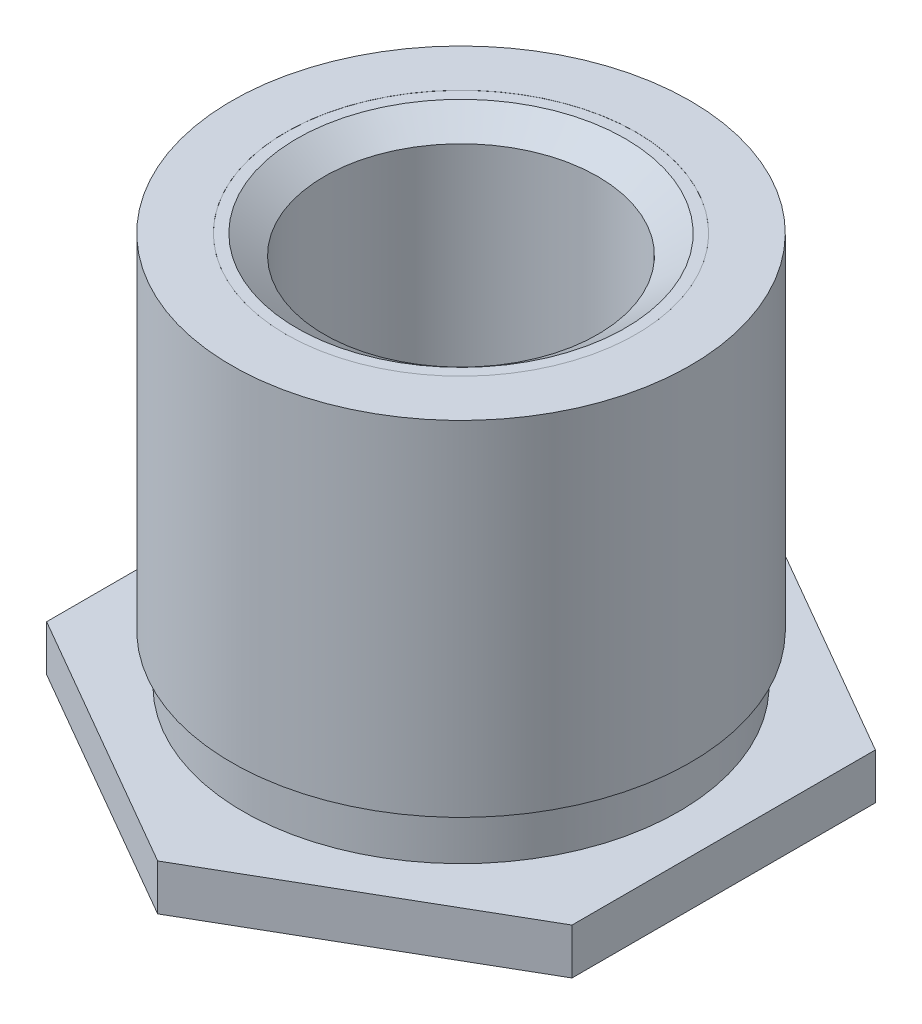
SolidWorks part; units mm, degrees
ref_plane "Plane1" through (0, 0, 0) normal (0, 0, 1) x (1, 0, 0)
ref_plane "Plane2" through (0, 0, 0) normal (0, 1, 0) x (1, 0, 0)
ref_plane "Plane3" through (0, 0, 0) normal (1, 0, 0) x (0, 0, -1)
sketch "BodySke" plane through (0, 0, 0) normal (0, 0, 1) x (1, 0, 0)
  line L0 (2.095, 0) -> (2.784, 0)
  line L1 (2.784, 0) -> (2.784, 0.419)
  line L2 (2.784, 0.419) -> (1.9903, 0.419)
  line L3 (1.25, 4) -> (1.25, 0.006)
  line L4 (2.095, 0.8589) -> (1.9903, 0.8589)
  line L5 (1.9903, 0.8589) -> (1.9903, 0.419)
  line L6 (2.095, 0.0025) -> (2.095, 0)
  line L7 (1.016, 3.5) -> (3.6522, 3.5) construction
  line L8 (2.095, 4) -> (1.25, 4)
  line L9 (0, 0) -> (0, 15.24) construction
  line L10 (2.095, 0.0025) -> (0, 0.0025)
  line L11 (2.095, 4) -> (2.095, 0.8589)
  line L12 (0, 0.006) -> (1.25, 0.006)
  line L13 (0, 0.006) -> (0, 0.0025)
  line L14 (1.016, 0.006) -> (3.6522, 0.006) construction
  line L15 (1.016, 0) -> (3.6522, 0) construction
  dimension "D1" = 0.0025
  dimension "E_dia" = 5.568
  dimension "C_dia" = 4.19
  dimension "Thread_min" = 2.5
  dimension "Clinching_ht" = 0.419
  dimension "Advance" = 0.5
  dimension "Length" = 4
  dimension "Thread_limit" = 3.994
  dimension "Thread_depth" = 3.994
  dimension "Drill_depth" = 4
  dimension "Groove_wid" = 0.44
  dimension "Groove_dia" = 3.9805
revolve "Body" add sketch "BodySke"
cosmetic thread "ThreadCosmetic" [suppressed]
revolve "EndChamfer" cut sketch "EndChamferSke" angle 360 about L0
sketch "EndChamferSke" plane through (0, 0, 0) normal (0, 0, 1) x (1, 0, 0)
  line L0 (0, -2.54) -> (0, 7.62) construction
  line L1 (0, 0) -> (0, 15.24) construction
  line L2 (1.6, 3.999) -> (1.6, 4.254)
  line L4 (1.6, 3.999) -> (1.5, 3.999)
  line L6 (1.5, 3.999) -> (1.25, 3.824)
  line L8 (1.25, 3.824) -> (1.25, 4.254)
  line L9 (1.6, 4.254) -> (1.25, 4.254)
  line L10 (2.095, 4) -> (-2.095, 4) construction
  dimension "D1" = 0.254
  dimension "Thread_nominal" = 3
  dimension "D2" = 34.99
  dimension "Thread_min" = 2.5
  dimension "Inset" = 0.001
  dimension "B_dia" = 3.2
revolve "TapDrill" cut sketch "TapDriSke" angle 360 about L0
sketch "TapDriSke" plane through (0, 0, 0) normal (0, 0, 1) x (1, 0, 0)
  line L0 (0, 0) -> (0, 15.24) construction
  line L1 (0, 0) -> (0, 15.24) construction
  line L2 (1.25, -2.494) -> (1.25, 4)
  line L3 (2.095, 4) -> (-2.095, 4) construction
  line L4 (1.25, -2.494) -> (0, -3.0118)
  line L5 (0, -3.0118) -> (0, 4)
  line L6 (0, 4) -> (1.25, 4)
  line L7 (1.25, 0.006) -> (1.25, 4) construction
  line L8 (0, -3.0118) -> (-1.25, -2.494) construction
  line L9 (-1.25, 4) -> (-1.25, 0.006) construction
  dimension "D1" = 135
  dimension "Depth" = 6.494
ref_plane "Plane4" through (0, -0.5486, 0) normal (0, 1, 0) x (-1, 0, 0)
sketch "ThdSchSke" [suppressed] plane through (0, 0, 0) normal (0, 0, 1) x (1, 0, 0)
  line L0 (0, -5.08) -> (0, 7.62) construction
  line L1 (0, 0) -> (0, 15.24) construction
  line L2 (0, 12) -> (2.5, 12) construction
  line L4 (2.5, 12) -> (2.1, 12.2801)
  line L5 (2.675, 12) -> (-2.675, 12) construction
  line L6 (2.5, 12) -> (2.1, 11.7199)
  line L7 (2.1, 12.2801) -> (2.1, 11.7199)
  dimension "Vee_angle" = 70
  dimension "Thread_nominal" = 3
  dimension "Thread_min" = 2.5
revolve "ThreadSchematic" [suppressed] cut sketch "ThdSchSke" angle 360 about L0
pattern_linear "ThdSchPat" [suppressed]
sketch "HexDieSke" plane through (0, 0.419, 0) normal (0, 1, 0) x (-1, 0, 0)
  line L0 (0, 2.7713) -> (2.4, 1.3856)
  line L1 (2.4, 1.3856) -> (2.4, -1.3856)
  line L2 (2.4, -1.3856) -> (0, -2.7713)
  line L3 (0, -2.7713) -> (-2.4, -1.3856)
  line L4 (-2.4, -1.3856) -> (-2.4, 1.3856)
  line L5 (-2.4, 1.3856) -> (0, 2.7713)
  circle A1 centre (0, 0) radius 2.4 construction
  circle A2 centre (0, 0) radius 2.7713 construction
  circle A3 centre (0, 0) radius 2.7845
  dimension "Width_across_flats" = 4.8
  dimension "OD" = 5.569
extrude "HexDie" cut sketch "HexDieSke" against normal blind 0.419
equation "' \"Length@BodySke\" = 20"
equation "' \"B_dia@EndChamferSke\" = 5.35"
equation "' \"C_dia@BodySke\" = 7.12"
equation "' \"Width_across_flats@HexDieSke\" = 7.9"
equation "' \"Inset@EndChamferSke\" = 8"
equation "' \"Advance@BodySke\" = 0.8"
equation "' \"Thread_min@BodySke\" = 4.2"
equation "' \"Thread_nominal@ThreadCosmetic\" = 5"
equation "\"E_dia@BodySke\" = \"Width_across_flats@HexDieSke\" * 1.16"
equation "\"Drill_depth@BodySke\" = \"Length@BodySke\""
equation "\"Thread_depth@BodySke\" = \"Length@BodySke\" - 0.006"
equation "\"Clinching_ht@BodySke\" = \"C_dia@BodySke\" * 0.1"
equation "\"Groove_dia@BodySke\" = \"C_dia@BodySke\" * 0.95"
equation "\"Groove_wid@BodySke\" = \"Clinching_ht@BodySke\" * 1.05"
equation "\"Thread_limit@BodySke\" = ((sgn( \"Length@BodySke\" - \"Thread_depth@BodySke\" )-1)*( \"Length@BodySke\" - \"Thread_depth@BodySke\" ))/-2+ \"Thread_depth@BodySke\""
equation "\"Depth@TapDriSke\" = \"Thread_limit@BodySke\" + \"Advance@BodySke\" * 5"
equation "\"Depth@TapDriSke\" = ((sgn( \"Depth@TapDriSke\" - \"Drill_depth@BodySke\" )+1)*( \"Depth@TapDriSke\" - \"Drill_depth@BodySke\" ))/2 +\"Drill_depth@BodySke\""
equation "\"Depth@HexDie\" = \"Clinching_ht@BodySke\""
equation "\"OD@HexDieSke\" =  \"Width_across_flats@HexDieSke\" * 1.16 + 0.001"
equation "\"Thread_nominal@EndChamferSke\" = \"Thread_nominal@ThreadCosmetic\""
equation "\"Thread_min@EndChamferSke\" = \"Thread_min@BodySke\""
equation "\"D2@EndChamferSke\" = \"Vee_angle@ThdSchSke\" / 2 - 0.01"
equation "\"Thread_nominal@ThdSchSke\" = \"Thread_nominal@ThreadCosmetic\""
equation "\"Thread_min@ThdSchSke\" = \"Thread_min@BodySke\""
equation "\"Num_threads@ThdSchPat\" = int(  ( \"Thread_limit@BodySke\" - \"Inset@EndChamferSke\" ) / \"Advance@BodySke\" + 0.999 )  + 1"
equation "\"Advance@ThdSchPat\" = (  \"Thread_limit@BodySke\" - \"Inset@EndChamferSke\" ) /  (\"Num_threads@ThdSchPat\" - 1) 'relax it"
